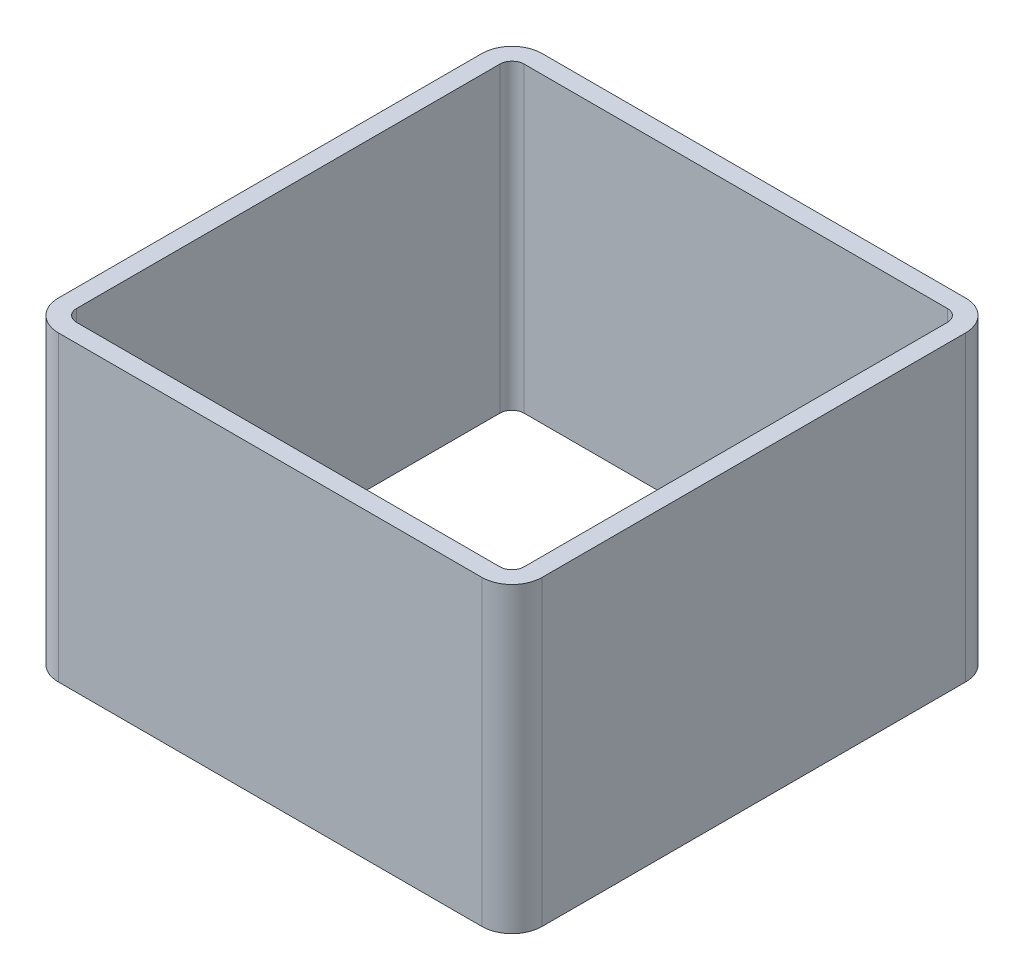
SolidWorks part; units mm, degrees
ref_plane "Спереди" through (0, 0, 0) normal (0, 0, 1) x (1, 0, 0)
ref_plane "Сверху" through (0, 0, 0) normal (0, 1, 0) x (1, 0, 0)
ref_plane "Справа" through (0, 0, 0) normal (1, 0, 0) x (0, 0, -1)
sketch "Эскиз1" plane through (0, 0, 0) normal (0, 1, 0) x (1, 0, 0)
  line L1 (-35, 40) -> (35, 40)
  line L2 (-40, 35) -> (-40, -35)
  line L3 (-35, -40) -> (35, -40)
  line L4 (40, 35) -> (40, -35)
  line L5 (-40, 40) -> (40, -40) construction
  line L6 (-40, -40) -> (40, 40) construction
  arc A0 (-40, -35) -> (-35, -40) centre (-35, -35) ccw
  arc A1 (35, -40) -> (40, -35) centre (35, -35) ccw
  arc A2 (35, 40) -> (40, 35) centre (35, 35) cw
  arc A3 (-35, 40) -> (-40, 35) centre (-35, 35) ccw
  point P0 (0, 0)
  dimension "D1" = 5
extrude "Вытянуть-Тонкостенный1" add sketch "Эскиз1" along normal blind 50 thin
